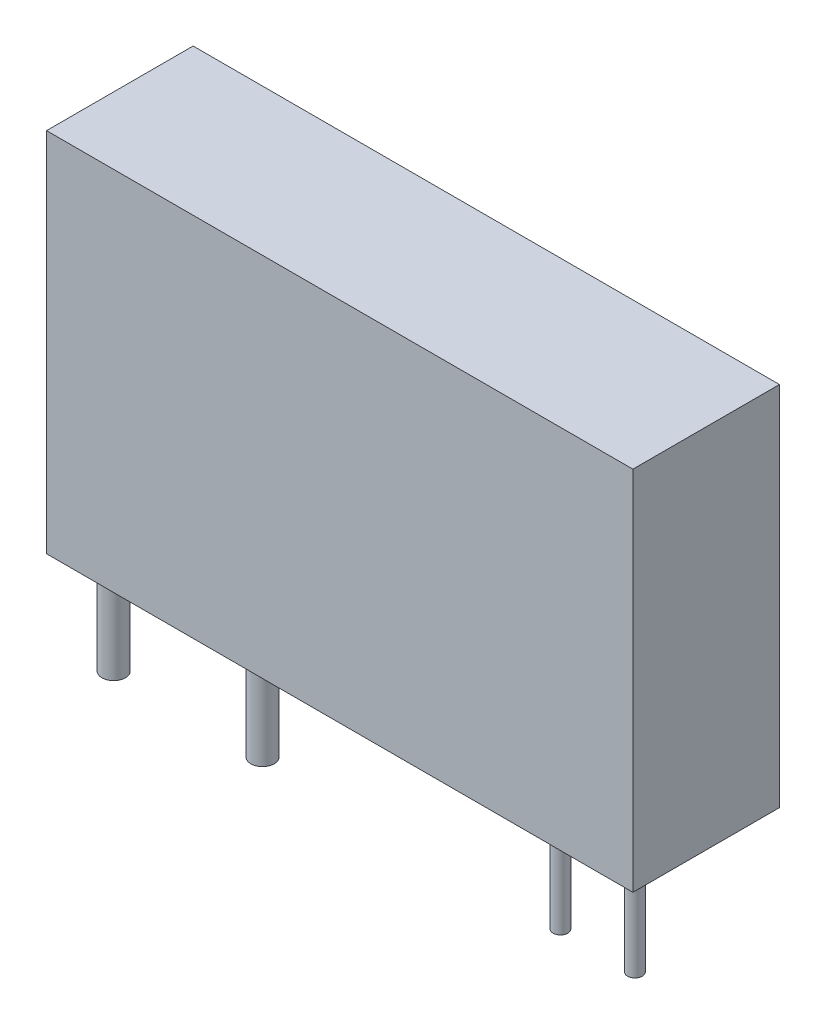
SolidWorks part; units mm, degrees
ref_plane "Alzado" through (0, 0, 0) normal (0, 0, 1) x (1, 0, 0)
ref_plane "Planta" through (0, 0, 0) normal (0, 1, 0) x (1, 0, 0)
ref_plane "Vista lateral" through (0, 0, 0) normal (1, 0, 0) x (0, 0, -1)
sketch "Croquis1" plane through (0, 0, 0) normal (0, 1, 0) x (1, 0, 0)
  line L2 (10, -2.5) -> (-10, -2.5)
  line L3 (10, -2.5) -> (10, 2.5)
  line L4 (10, 2.5) -> (-10, 2.5)
  line L5 (-10, -2.5) -> (-10, 2.5)
  line L6 (10, -2.5) -> (-10, 2.5) construction
  line L7 (10, 2.5) -> (-10, -2.5) construction
  point P2 (0, 0)
extrude "Saliente-Extruir1" add sketch "Croquis1" along normal blind 12.5
sketch "Croquis2" plane through (0, 0, 0) normal (0, -1, 0) x (-1, 0, 0)
  line L0 (0, 0) -> (-8.89, 0) construction
  line L1 (-8.89, 0) -> (-6.35, 0) construction
  line L2 (0, 0) -> (8.89, 0) construction
  line L3 (8.89, 0) -> (3.81, 0) construction
  circle A0 centre (-8.89, 0) radius 0.25
  circle A1 centre (-6.35, 0) radius 0.25
  circle A2 centre (3.81, 0) radius 0.4
  circle A3 centre (8.89, 0) radius 0.4
sketch "Croquis4" plane through (0, 0, 0) normal (0, -1, 0) x (1, 0, 0)
  line L0 (8.89, 0) -> (8.89, 2.5) construction
  line L1 (-10, 2.5) -> (10, 2.5) construction
  line L2 (8.89, 2.5) -> (8.89, 1.32) construction
  line L3 (8.89, 1.32) -> (-10, 1.32) construction
  line L4 (-10, -2.5) -> (-10, 2.5) construction
  line L5 (-8.89, 0) -> (-8.89, 1.32) construction
  line L6 (-8.89, 1.32) -> (-3.81, 1.32) construction
  line L7 (-3.81, 1.32) -> (6.35, 1.32) construction
  circle A0 centre (-8.89, 1.32) radius 0.4
  circle A1 centre (-3.81, 1.32) radius 0.4
  circle A2 centre (6.35, 1.32) radius 0.25
  circle A3 centre (8.89, 1.32) radius 0.25
extrude "Saliente-Extruir3" add sketch "Croquis4" along normal blind 3.5
